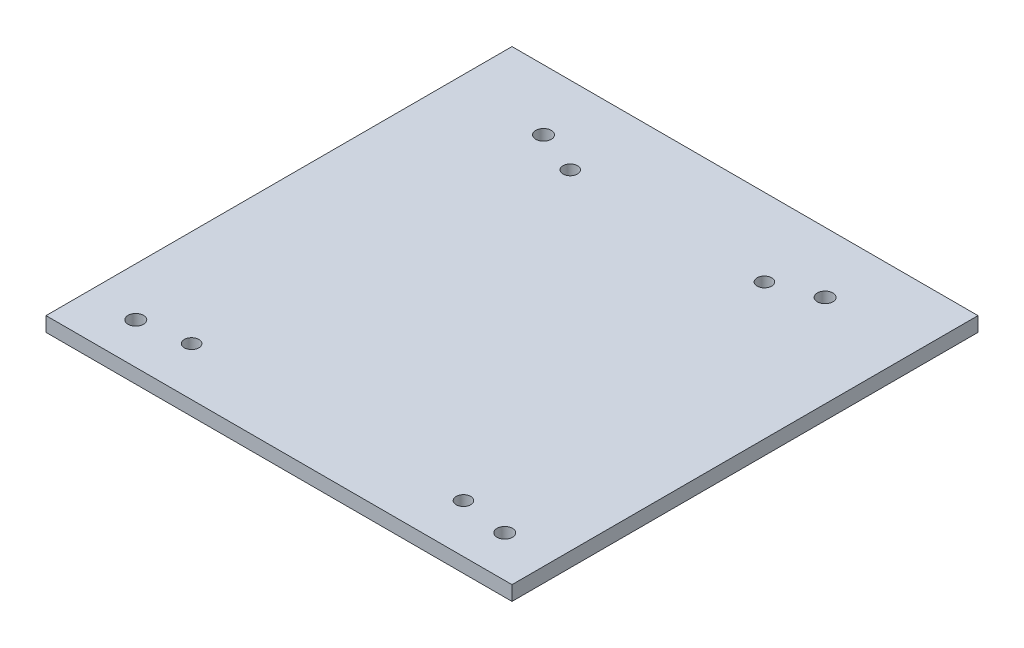
SolidWorks part; units mm, degrees
ref_plane "Front Plane" through (0, 0, 0) normal (0, 0, 1) x (1, 0, 0)
ref_plane "Top Plane" through (0, 0, 0) normal (0, 1, 0) x (1, 0, 0)
ref_plane "Right Plane" through (0, 0, 0) normal (1, 0, 0) x (0, 0, -1)
sketch "Sketch1" plane through (0, 0, 0) normal (0, 1, 0) x (1, 0, 0)
  line L1 (0, 0) -> (96, 0)
  line L2 (0, 0) -> (0, 96)
  line L3 (0, 96) -> (96, 96)
  line L4 (96, 0) -> (96, 96)
  circle A0 centre (19, 83.5) radius 1.6
  circle A1 centre (77, 83.5) radius 1.6
  circle A2 centre (10, 8.5) radius 1.6
  circle A3 centre (86, 8.5) radius 1.6
  circle A4 centre (28, 80) radius 1.5
  circle A5 centre (68, 80) radius 1.5
  circle A6 centre (20, 10) radius 1.5
  circle A7 centre (76, 10) radius 1.5
  dimension "D3" = 3.2
  dimension "D4" = 3.2
  dimension "D5" = 3.2
  dimension "D6" = 3.2
  dimension "D7" = 12.5
  dimension "D8" = 12.5
  dimension "D9" = 86
  dimension "D10" = 10
  dimension "D11" = 77
  dimension "D13" = 75
  dimension "D15" = 3
  dimension "D16" = 3
  dimension "D17" = 3
  dimension "D18" = 3
  dimension "D21" = 10
  dimension "D1" = 96
  dimension "D2" = 96
  dimension "D12" = 19
  dimension "D14" = 75
  dimension "D19" = 56
  dimension "D20" = 70
  dimension "D22" = 20
  dimension "D23" = 40
  dimension "D24" = 28
extrude "Boss-Extrude1" add sketch "Sketch1" along normal blind 3
